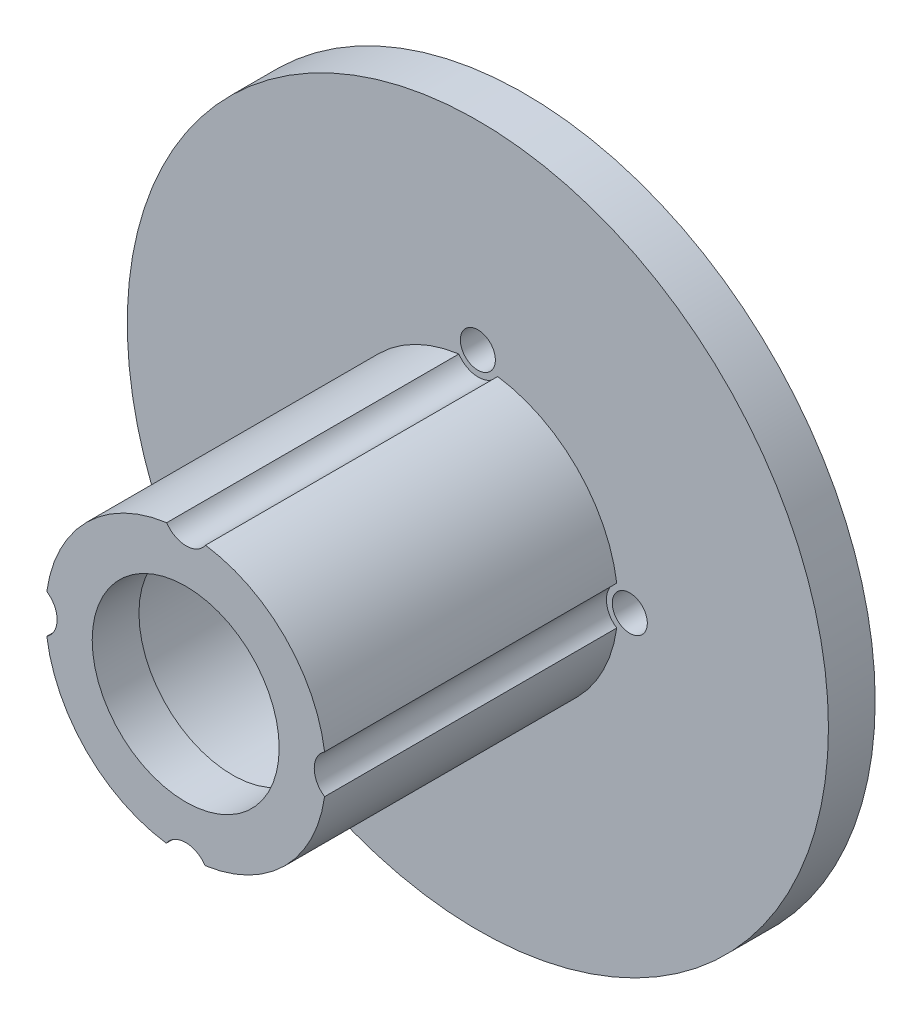
SolidWorks part; units mm, degrees
material "6063-T6"
ref_plane "Front Plane" through (0, 0, 0) normal (0, 0, 1) x (1, 0, 0)
ref_plane "Top Plane" through (0, 0, 0) normal (0, 1, 0) x (1, 0, 0)
ref_plane "Right Plane" through (0, 0, 0) normal (1, 0, 0) x (0, 0, -1)
sketch "Sketch2" plane through (0, 0, 0) normal (0, 0, 1) x (1, 0, 0)
  circle A0 centre (0, 0) radius 30
  dimension "D1" = 60
extrude "Boss-Extrude1" add sketch "Sketch2" along normal blind 4
sketch "Sketch3" plane through (0, 0, 4) normal (0, 0, 1) x (1, 0, 0)
  circle A0 centre (0, 0) radius 12
  dimension "D1" = 24
extrude "Boss-Extrude2" add sketch "Sketch3" along normal blind 25
sketch "Sketch4" plane through (0, 0, 0) normal (0, 0, -1) x (-1, 0, 0)
  circle A0 centre (0, 0) radius 9.5
  dimension "D1" = 19
extrude "Cut-Extrude1" cut sketch "Sketch4" against normal blind 25
sketch "Sketch5" plane through (0, 0, 25) normal (0, 0, -1) x (-1, 0, 0)
  circle A0 centre (0, 0) radius 8
  dimension "D1" = 16
extrude "Cut-Extrude2" cut sketch "Sketch5" against normal blind 20
sketch "Sketch6" plane through (0, 0, 0) normal (0, 0, -1) x (-1, 0, 0)
  circle A0 centre (0, 0) radius 13 construction
  circle A1 centre (0, 13) radius 1.5
  circle A2 centre (13, 0) radius 1.5
  circle A3 centre (0, -13) radius 1.5
  circle A4 centre (-13, 0) radius 1.5
  point P14 (0, 0)
  dimension "D1" = 26
  dimension "D2" = 3
  dimension "D3" = 4
extrude "Cut-Extrude10" cut sketch "Sketch6" against normal blind 4
sketch "Sketch8" plane through (0, 0, 29) normal (0, 0, 1) x (1, 0, 0)
  circle A0 centre (0.0399, 13) radius 2
  circle A1 centre (0, -13) radius 2
  circle A2 centre (13, 0) radius 2
  circle A3 centre (-13, 0) radius 2
  dimension "D1" = 4
  dimension "D2" = 4
  dimension "D3" = 4
  dimension "D4" = 4
  dimension "D5" = 13
  dimension "D6" = 13
  dimension "D7" = 13
  dimension "D8" = 13
extrude "Cut-Extrude14" cut sketch "Sketch8" against normal up to surface (25 mm away) up to face at (0, 0, 4)
